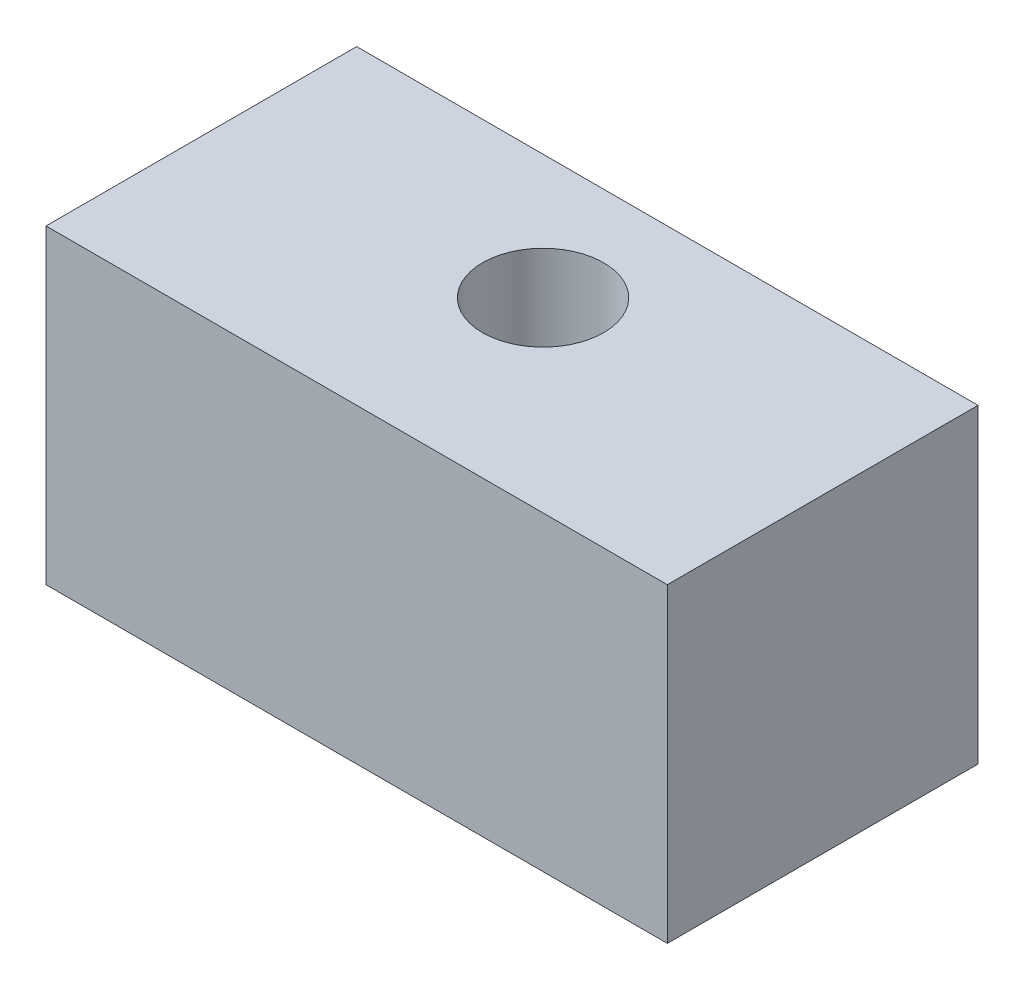
SolidWorks part; units mm, degrees
ref_plane "Front Plane" through (0, 0, 0) normal (0, 0, 1) x (1, 0, 0)
ref_plane "Top Plane" through (0, 0, 0) normal (0, 1, 0) x (1, 0, 0)
ref_plane "Right Plane" through (0, 0, 0) normal (1, 0, 0) x (0, 0, -1)
sketch "Sketch3" plane through (0, 0, 0) normal (0, 1, 0) x (1, 0, 0)
  line L1 (-10, 5) -> (10, 5)
  line L2 (-10, 5) -> (-10, -5)
  line L3 (-10, -5) -> (10, -5)
  line L4 (10, 5) -> (10, -5)
  line L5 (-10, 5) -> (10, -5) construction
  line L6 (-10, -5) -> (10, 5) construction
  point P0 (0, 0)
  dimension "D1" = 20
  dimension "D2" = 10
extrude "Boss-Extrude1" add sketch "Sketch3" along normal blind 10
sketch "Sketch4" plane through (0, 10, 0) normal (0, 1, 0) x (1, 0, 0)
  line L0 (10, 5) -> (-10, 5) construction
  circle A0 centre (0, 1) radius 1.95
  dimension "D1" = 4
extrude "Cut-Extrude1" cut sketch "Sketch4" against normal blind 10
